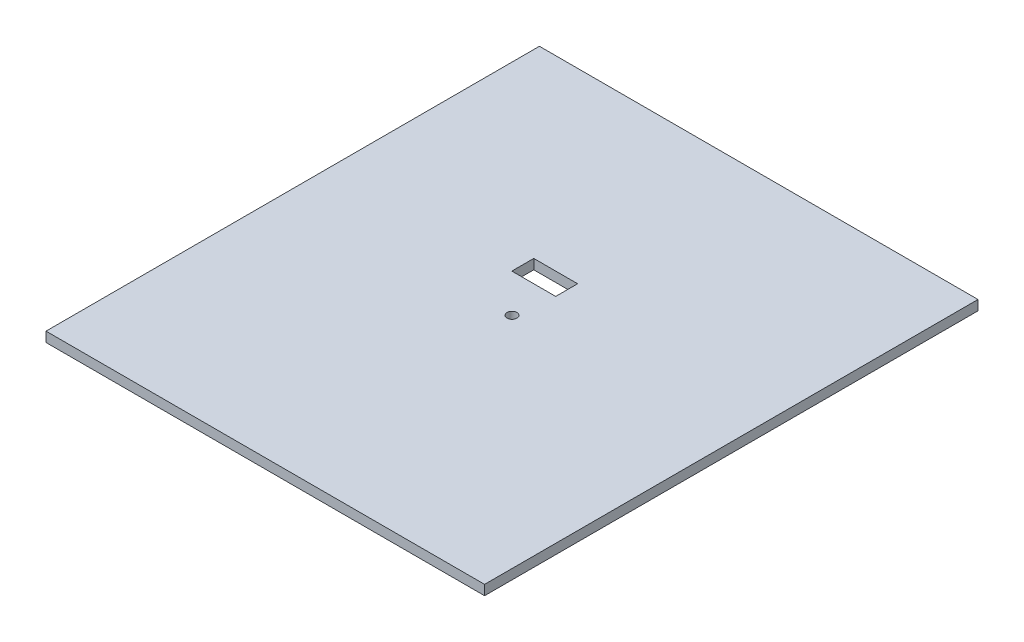
SolidWorks part; units mm, degrees
other "Markup1"
sketch "Sketch6" plane through (-216.6667, 9, -153.2051) normal (0, 1, 0) x (1, 0, 0)
ref_plane "Front Plane" through (0, 0, 0) normal (0, 0, 1) x (1, 0, 0)
ref_plane "Top Plane" through (0, 0, 0) normal (0, 1, 0) x (1, 0, 0)
ref_plane "Right Plane" through (0, 0, 0) normal (1, 0, 0) x (0, 0, -1)
sketch "Sketch1" plane through (0, 0, 0) normal (0, 1, 0) x (1, 0, 0)
  line L0 (-216.6667, 153.2051) -> (183.3333, 153.2051)
  line L1 (183.3333, 153.2051) -> (183.3333, -296.7949)
  line L2 (183.3333, -296.7949) -> (-216.6667, -296.7949)
  line L3 (-216.6667, -296.7949) -> (-216.6667, 153.2051)
  dimension "D1" = 400
  dimension "D2" = 450
extrude "Boss-Extrude5" add sketch "Sketch1" along normal blind 9
sketch "Sketch4" plane through (0, 0, 0) normal (0, 1, 0) x (1, 0, 0)
  line L0 (183.3333, -296.7949) -> (183.3333, 153.2051) construction
  line L1 (183.3333, 153.2051) -> (-216.6667, 153.2051) construction
  circle A0 centre (-16.6667, -71.7949) radius 12.5
  circle A2 centre (-16.6667, -71.7949) radius 4.5
  dimension "D3" = 25
  dimension "D4" = 9
  dimension "D1" = 200
  dimension "D2" = 225
extrude "Cut-Extrude2" cut sketch "Sketch4" along normal blind 9 contours A2
sketch "Sketch5" plane through (0, 0, 0) normal (0, -1, 0) x (-1, 0, 0)
  line L1 (11.6667, -36.9459) -> (51.6667, -36.9459)
  line L2 (11.6667, -36.9459) -> (11.6667, -16.9459)
  line L3 (11.6667, -16.9459) -> (51.6667, -16.9459)
  line L4 (51.6667, -36.9459) -> (51.6667, -16.9459)
  line L5 (216.6667, 153.2051) -> (216.6667, -296.7949) construction
  dimension "D1" = 40
  dimension "D2" = 20
  dimension "D3" = 165
extrude "Cut-Extrude3" cut sketch "Sketch5" against normal blind 9
sketch3d "3DSketch1"
  line L0 (-51.6667, 9, 36.9459) -> (-51.6667, 9, 16.9459) construction
  point P0 (-51.6667, 9, 0)
